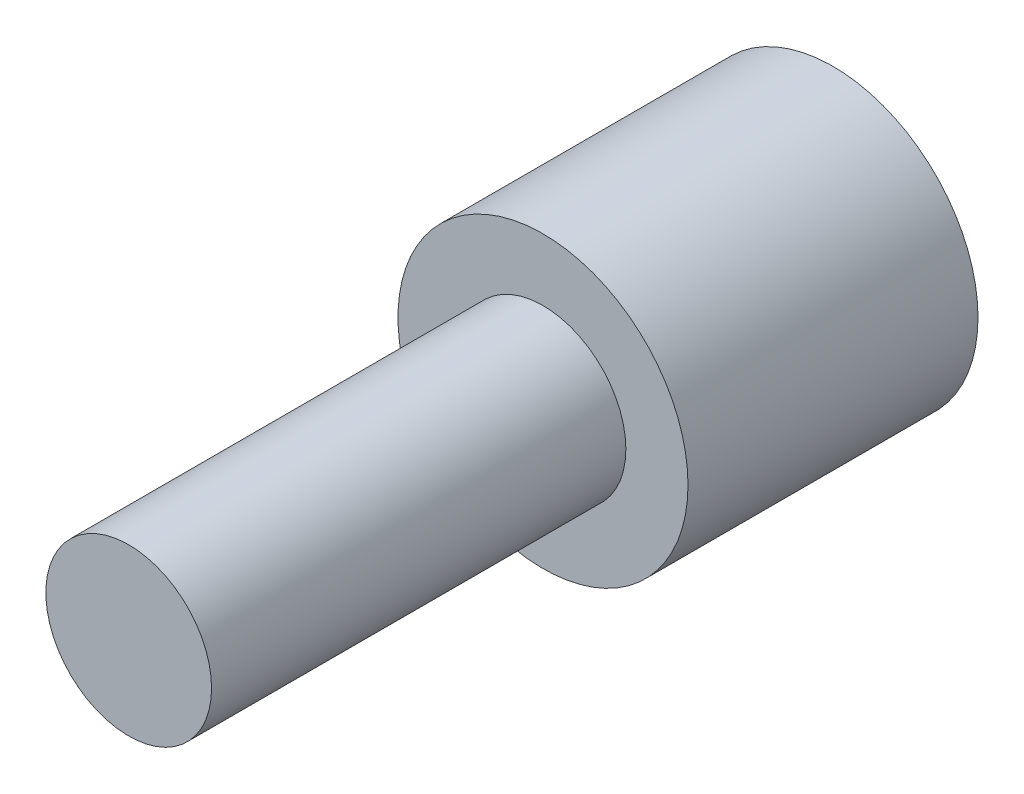
SolidWorks part; units mm, degrees
ref_plane "Plan de face" through (0, 0, 0) normal (0, 0, 1) x (1, 0, 0)
ref_plane "Plan de dessus" through (0, 0, 0) normal (0, 1, 0) x (1, 0, 0)
ref_plane "Plan de droite" through (0, 0, 0) normal (1, 0, 0) x (0, 0, -1)
sketch "Esquisse1" plane through (0, 0, 0) normal (0, 0, 1) x (1, 0, 0)
  circle A0 centre (0, 0) radius 3.5
  dimension "D1" = 7
extrude "Boss.-Extru.1" add sketch "Esquisse1" along normal blind 7
sketch "Esquisse2" plane through (0, 0, 0) normal (0, 0, -1) x (-1, 0, 0)
  circle A0 centre (0, 0) radius 2.9
  dimension "D1" = 5.8
extrude "Enlèv. mat.-Extru.1" cut sketch "Esquisse2" against normal blind 2.5
sketch "Esquisse3" plane through (0, 0, 7) normal (0, 0, 1) x (1, 0, 0)
  circle A0 centre (0, 0) radius 2
  dimension "D1" = 4
extrude "Boss.-Extru.2" add sketch "Esquisse3" along normal blind 10
